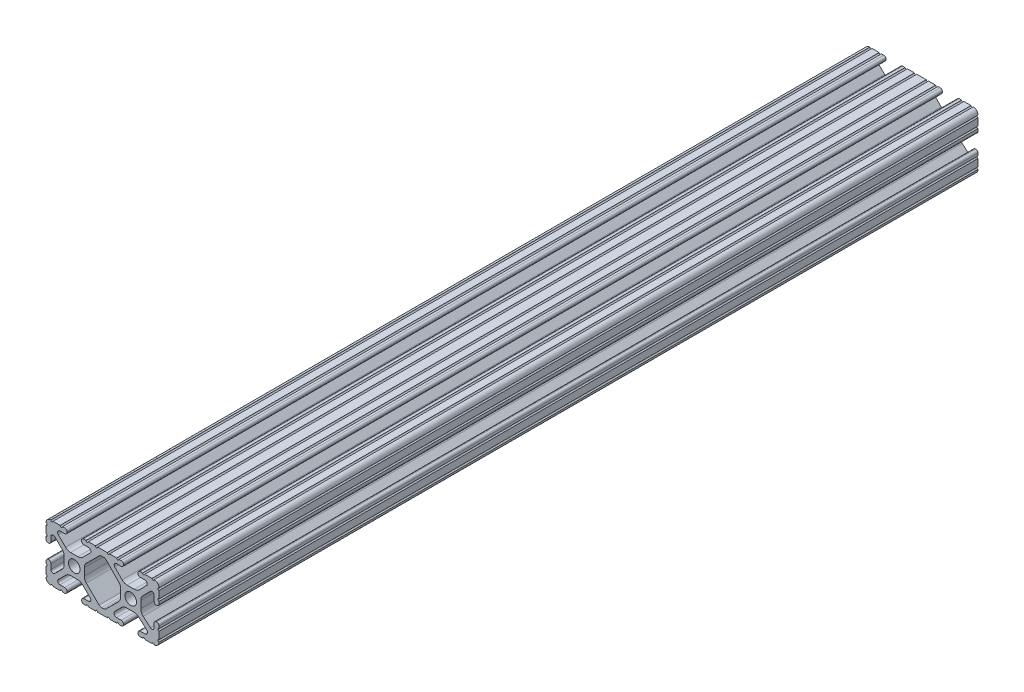
SolidWorks part; units mm, degrees
ref_plane "Front Plane" through (0, 0, 0) normal (0, 0, 1) x (1, 0, 0)
ref_plane "Top Plane" through (0, 0, 0) normal (0, 1, 0) x (1, 0, 0)
ref_plane "Right Plane" through (0, 0, 0) normal (1, 0, 0) x (0, 0, -1)
sketch "Sketch1" plane through (0, 0, 0) normal (0, 0, 1) x (1, 0, 0)
  line L0 (-7.2595, -3.8694) -> (-1.5457, -9.5728)
  line L1 (-8.1915, 1.6223) -> (-8.1915, -1.6223)
  line L2 (-1.504, 9.5765) -> (-7.252, 3.8768)
  line L3 (0.5515, 10.033) -> (-0.3952, 10.033)
  line L4 (7.2829, 3.8459) -> (1.6756, 9.5611)
  line L5 (8.1915, -1.6223) -> (8.1915, 1.6223)
  line L6 (1.5457, -9.5728) -> (7.2595, -3.8694)
  line L7 (-0.4332, -10.033) -> (0.4332, -10.033)
  line L8 (18.0171, 12.7) -> (16.9875, 12.7)
  line L9 (15.9385, 11.651) -> (15.9385, 11.5392)
  line L10 (16.9875, 10.4902) -> (19.1164, 10.4902)
  line L11 (19.8441, 8.7652) -> (16.619, 5.4551)
  line L12 (14.3449, 4.4958) -> (11.0833, 4.4958)
  line L13 (8.817, 5.4472) -> (5.5642, 8.7627)
  line L14 (6.2894, 10.4902) -> (8.4125, 10.4902)
  line L15 (9.4615, 11.5392) -> (9.4615, 11.651)
  line L16 (8.4125, 12.7) -> (7.3829, 12.7)
  line L17 (6.3669, 12.7) -> (3.1496, 12.7)
  line L18 (2.1336, 12.7) -> (-2.1336, 12.7)
  line L19 (-3.1496, 12.7) -> (-6.3669, 12.7)
  line L20 (-7.3829, 12.7) -> (-8.4125, 12.7)
  line L21 (-9.4615, 11.651) -> (-9.4615, 11.5392)
  line L22 (-8.4125, 10.4902) -> (-6.2836, 10.4902)
  line L23 (-5.5326, 8.6661) -> (-8.81, 5.4163)
  line L24 (-11.0455, 4.4958) -> (-14.3545, 4.4958)
  line L25 (-16.59, 5.4163) -> (-19.8674, 8.6661)
  line L26 (-19.1164, 10.4902) -> (-16.9875, 10.4902)
  line L27 (-15.9385, 11.5392) -> (-15.9385, 11.651)
  line L28 (-16.9875, 12.7) -> (-18.0171, 12.7)
  line L29 (-19.0331, 12.7) -> (-22.2504, 12.7)
  line L30 (-25.4, 9.5504) -> (-25.4, 6.3331)
  line L31 (-25.4, 5.3171) -> (-25.4, 4.2375)
  line L32 (-24.401, 3.2385) -> (-24.2392, 3.2385)
  line L33 (-23.1902, 4.2875) -> (-23.1902, 6.3347)
  line L34 (-21.434, 7.0665) -> (-18.148, 3.8082)
  line L35 (-17.2085, 1.5536) -> (-17.2085, -1.6952)
  line L36 (-18.1405, -3.9423) -> (-21.4316, -7.2274)
  line L37 (-23.1902, -6.498) -> (-23.1902, -4.2875)
  line L38 (-24.2392, -3.2385) -> (-24.351, -3.2385)
  line L39 (-25.4, -4.2875) -> (-25.4, -5.3171)
  line L40 (-25.4, -6.3331) -> (-25.4, -9.5504)
  line L41 (-22.2504, -12.7) -> (-19.0331, -12.7)
  line L42 (-18.0171, -12.7) -> (-16.9875, -12.7)
  line L43 (-15.9384, -11.651) -> (-15.9384, -11.5392)
  line L44 (-16.9875, -10.4902) -> (-19.1164, -10.4902)
  line L45 (-19.8341, -8.7551) -> (-16.4966, -5.4237)
  line L46 (-14.2536, -4.4958) -> (-11.1464, -4.4958)
  line L47 (-8.9034, -5.4237) -> (-5.5659, -8.7551)
  line L48 (-6.2836, -10.4902) -> (-8.4125, -10.4902)
  line L49 (-9.4616, -11.5392) -> (-9.4616, -11.651)
  line L50 (-8.4125, -12.7) -> (-7.3829, -12.7)
  line L51 (-6.3669, -12.7) -> (-3.1496, -12.7)
  line L52 (-2.1336, -12.7) -> (2.1336, -12.7)
  line L53 (3.1496, -12.7) -> (6.3669, -12.7)
  line L54 (7.3829, -12.7) -> (8.4125, -12.7)
  line L55 (9.4616, -11.651) -> (9.4616, -11.5392)
  line L56 (8.4125, -10.4902) -> (6.2894, -10.4902)
  line L57 (5.4807, -8.5353) -> (8.5979, -5.4237)
  line L58 (10.8409, -4.4958) -> (14.1026, -4.4958)
  line L59 (16.1879, -5.2766) -> (19.8682, -8.4822)
  line L60 (19.1164, -10.4902) -> (16.9875, -10.4902)
  line L61 (15.9384, -11.5392) -> (15.9384, -11.651)
  line L62 (16.9875, -12.7) -> (18.0171, -12.7)
  line L63 (19.0331, -12.7) -> (22.2504, -12.7)
  line L64 (25.4, -9.5504) -> (25.4, -6.3331)
  line L65 (25.4, -5.3171) -> (25.4, -4.2375)
  line L66 (24.401, -3.2385) -> (24.1892, -3.2385)
  line L67 (23.1902, -4.2375) -> (23.1902, -6.1559)
  line L68 (21.584, -6.8869) -> (18.2982, -4.025)
  line L69 (17.2085, -1.6308) -> (17.2085, 1.6308)
  line L70 (18.1094, 3.8465) -> (21.5263, 7.3534)
  line L71 (23.1902, 6.6769) -> (23.1902, 4.2375)
  line L72 (24.1892, 3.2385) -> (24.401, 3.2385)
  line L73 (25.4, 4.2375) -> (25.4, 5.3171)
  line L74 (25.4, 6.3332) -> (25.4, 9.5504)
  line L75 (22.2504, 12.7) -> (19.0331, 12.7)
  circle A0 centre (-12.7, 0) radius 2.6035
  circle A1 centre (12.7, 0) radius 2.6035
  arc A2 (-1.5457, -9.5728) -> (-0.4332, -10.033) centre (-0.4332, -8.4582) ccw
  arc A3 (-8.1915, -1.6223) -> (-7.2595, -3.8694) centre (-5.0165, -1.6223) ccw
  arc A4 (-7.252, 3.8768) -> (-8.1915, 1.6223) centre (-5.0165, 1.6223) ccw
  arc A5 (-0.3952, 10.033) -> (-1.504, 9.5765) centre (-0.3952, 8.4582) ccw
  arc A6 (1.6756, 9.5611) -> (0.5515, 10.033) centre (0.5515, 8.4582) ccw
  arc A7 (8.1915, 1.6223) -> (7.2829, 3.8459) centre (5.0165, 1.6223) ccw
  arc A8 (7.2595, -3.8694) -> (8.1915, -1.6223) centre (5.0165, -1.6223) ccw
  arc A9 (0.4332, -10.033) -> (1.5457, -9.5728) centre (0.4332, -8.4582) ccw
  arc A10 (18.0171, 12.7) -> (19.0331, 12.7) centre (18.5251, 12.7) ccw
  arc A11 (16.9875, 12.7) -> (15.9385, 11.651) centre (16.9875, 11.651) ccw
  arc A12 (15.9385, 11.5392) -> (16.9875, 10.4902) centre (16.9875, 11.5392) ccw
  arc A13 (19.8441, 8.7652) -> (19.1164, 10.4902) centre (19.1164, 9.4742) ccw
  arc A14 (14.3449, 4.4958) -> (16.619, 5.4551) centre (14.3449, 7.6708) ccw
  arc A15 (8.817, 5.4472) -> (11.0833, 4.4958) centre (11.0833, 7.6708) ccw
  arc A16 (6.2894, 10.4902) -> (5.5642, 8.7627) centre (6.2894, 9.4742) ccw
  arc A17 (8.4125, 10.4902) -> (9.4615, 11.5392) centre (8.4125, 11.5392) ccw
  arc A18 (9.4615, 11.651) -> (8.4125, 12.7) centre (8.4125, 11.651) ccw
  arc A19 (6.3669, 12.7) -> (7.3829, 12.7) centre (6.8749, 12.7) ccw
  arc A20 (2.1336, 12.7) -> (3.1496, 12.7) centre (2.6416, 12.7) ccw
  arc A21 (-3.1496, 12.7) -> (-2.1336, 12.7) centre (-2.6416, 12.7) ccw
  arc A22 (-7.3829, 12.7) -> (-6.3669, 12.7) centre (-6.8749, 12.7) ccw
  arc A23 (-8.4125, 12.7) -> (-9.4615, 11.651) centre (-8.4125, 11.651) ccw
  arc A24 (-9.4615, 11.5392) -> (-8.4125, 10.4902) centre (-8.4125, 11.5392) ccw
  arc A25 (-5.5326, 8.6661) -> (-6.2836, 10.4902) centre (-6.2836, 9.4235) ccw
  arc A26 (-11.0455, 4.4958) -> (-8.81, 5.4163) centre (-11.0455, 7.6708) ccw
  arc A27 (-16.59, 5.4163) -> (-14.3545, 4.4958) centre (-14.3545, 7.6708) ccw
  arc A28 (-19.1164, 10.4902) -> (-19.8674, 8.6661) centre (-19.1164, 9.4235) ccw
  arc A29 (-16.9875, 10.4902) -> (-15.9385, 11.5392) centre (-16.9875, 11.5392) ccw
  arc A30 (-15.9385, 11.651) -> (-16.9875, 12.7) centre (-16.9875, 11.651) ccw
  arc A31 (-19.0331, 12.7) -> (-18.0171, 12.7) centre (-18.5251, 12.7) ccw
  arc A32 (-23.2664, 12.6998) -> (-22.2504, 12.7) centre (-22.7584, 12.7) ccw
  arc A33 (-23.2664, 12.6998) -> (-25.3998, 10.5664) centre (-23.2918, 10.5918) ccw
  arc A34 (-25.4, 9.5504) -> (-25.3998, 10.5664) centre (-25.4, 10.0584) ccw
  arc A35 (-25.4, 5.3171) -> (-25.4, 6.3331) centre (-25.4, 5.8251) ccw
  arc A36 (-25.4, 4.2375) -> (-24.401, 3.2385) centre (-24.401, 4.2375) ccw
  arc A37 (-24.2392, 3.2385) -> (-23.1902, 4.2875) centre (-24.2392, 4.2875) ccw
  arc A38 (-21.434, 7.0665) -> (-23.1902, 6.3347) centre (-22.1596, 6.3347) ccw
  arc A39 (-17.2085, 1.5536) -> (-18.148, 3.8082) centre (-20.3835, 1.5536) ccw
  arc A40 (-18.1405, -3.9423) -> (-17.2085, -1.6952) centre (-20.3835, -1.6952) ccw
  arc A41 (-23.1902, -6.498) -> (-21.4316, -7.2274) centre (-22.1596, -6.498) ccw
  arc A42 (-23.1902, -4.2875) -> (-24.2392, -3.2385) centre (-24.2392, -4.2875) ccw
  arc A43 (-24.351, -3.2385) -> (-25.4, -4.2875) centre (-24.351, -4.2875) ccw
  arc A44 (-25.4, -6.3331) -> (-25.4, -5.3171) centre (-25.4, -5.8251) ccw
  arc A45 (-25.3998, -10.5664) -> (-25.4, -9.5504) centre (-25.4, -10.0584) ccw
  arc A46 (-25.3998, -10.5664) -> (-23.2664, -12.6998) centre (-23.2918, -10.5918) ccw
  arc A47 (-22.2504, -12.7) -> (-23.2664, -12.6998) centre (-22.7584, -12.7) ccw
  arc A48 (-18.0171, -12.7) -> (-19.0331, -12.7) centre (-18.5251, -12.7) ccw
  arc A49 (-16.9875, -12.7) -> (-15.9384, -11.651) centre (-16.9875, -11.651) ccw
  arc A50 (-15.9384, -11.5392) -> (-16.9875, -10.4902) centre (-16.9875, -11.5392) ccw
  arc A51 (-19.8341, -8.7551) -> (-19.1164, -10.4902) centre (-19.1164, -9.4742) ccw
  arc A52 (-14.2536, -4.4958) -> (-16.4966, -5.4237) centre (-14.2536, -7.6708) ccw
  arc A53 (-8.9034, -5.4237) -> (-11.1464, -4.4958) centre (-11.1464, -7.6708) ccw
  arc A54 (-6.2836, -10.4902) -> (-5.5659, -8.7551) centre (-6.2836, -9.4742) ccw
  arc A55 (-8.4125, -10.4902) -> (-9.4616, -11.5392) centre (-8.4125, -11.5392) ccw
  arc A56 (-9.4616, -11.651) -> (-8.4125, -12.7) centre (-8.4125, -11.651) ccw
  arc A57 (-6.3669, -12.7) -> (-7.3829, -12.7) centre (-6.8749, -12.7) ccw
  arc A58 (-2.1336, -12.7) -> (-3.1496, -12.7) centre (-2.6416, -12.7) ccw
  arc A59 (3.1496, -12.7) -> (2.1336, -12.7) centre (2.6416, -12.7) ccw
  arc A60 (7.3829, -12.7) -> (6.3669, -12.7) centre (6.8749, -12.7) ccw
  arc A61 (8.4125, -12.7) -> (9.4616, -11.651) centre (8.4125, -11.651) ccw
  arc A62 (9.4616, -11.5392) -> (8.4125, -10.4902) centre (8.4125, -11.5392) ccw
  arc A63 (5.4807, -8.5353) -> (6.2894, -10.4902) centre (6.2894, -9.3455) ccw
  arc A64 (10.8409, -4.4958) -> (8.5979, -5.4237) centre (10.8409, -7.6708) ccw
  arc A65 (16.1879, -5.2766) -> (14.1026, -4.4958) centre (14.1026, -7.6708) ccw
  arc A66 (19.1164, -10.4902) -> (19.8682, -8.4822) centre (19.1164, -9.3455) ccw
  arc A67 (16.9875, -10.4902) -> (15.9384, -11.5392) centre (16.9875, -11.5392) ccw
  arc A68 (15.9384, -11.651) -> (16.9875, -12.7) centre (16.9875, -11.651) ccw
  arc A69 (19.0331, -12.7) -> (18.0171, -12.7) centre (18.5251, -12.7) ccw
  arc A70 (23.2664, -12.6998) -> (22.2504, -12.7) centre (22.7584, -12.7) ccw
  arc A71 (23.2664, -12.6998) -> (25.3998, -10.5664) centre (23.2918, -10.5918) ccw
  arc A72 (25.4, -9.5504) -> (25.3998, -10.5664) centre (25.4, -10.0584) ccw
  arc A73 (25.4, -5.3171) -> (25.4, -6.3331) centre (25.4, -5.8251) ccw
  arc A74 (25.4, -4.2375) -> (24.401, -3.2385) centre (24.401, -4.2375) ccw
  arc A75 (24.1892, -3.2385) -> (23.1902, -4.2375) centre (24.1892, -4.2375) ccw
  arc A76 (21.584, -6.8869) -> (23.1902, -6.1559) centre (22.2207, -6.1559) ccw
  arc A77 (17.2085, -1.6308) -> (18.2982, -4.025) centre (20.3835, -1.6308) ccw
  arc A78 (18.1094, 3.8465) -> (17.2085, 1.6308) centre (20.3835, 1.6308) ccw
  arc A79 (23.1902, 6.6769) -> (21.5263, 7.3534) centre (22.2207, 6.6769) ccw
  arc A80 (23.1902, 4.2375) -> (24.1892, 3.2385) centre (24.1892, 4.2375) ccw
  arc A81 (24.401, 3.2385) -> (25.4, 4.2375) centre (24.401, 4.2375) ccw
  arc A82 (25.4, 6.3332) -> (25.4, 5.3171) centre (25.4, 5.8251) ccw
  arc A83 (25.3998, 10.5664) -> (25.4, 9.5504) centre (25.4, 10.0584) ccw
  arc A84 (25.3998, 10.5664) -> (23.2664, 12.6998) centre (23.2918, 10.5918) ccw
  arc A85 (22.2504, 12.7) -> (23.2664, 12.6998) centre (22.7584, 12.7) ccw
  point P248 (0, 10.033)
extrude "Boss-Extrude1" add sketch "Sketch1" along normal mid plane 368.3
sketch "Sketch2" plane through (17.2085, 0, 0) normal (1, 0, 0) x (0, 0, -1)
  line L0 (0, 0) -> (0, 51.7748) construction
  circle A0 centre (39.6875, 0) radius 3.175
  circle A1 centre (65.0875, 0) radius 3.175
  circle A2 centre (-65.0875, 0) radius 3.175
  circle A3 centre (-39.6875, 0) radius 3.175
  point P7 (0, 0)
  dimension "D1" = 6.35
  dimension "D2" = 39.6875
  dimension "D3" = 6.35
  dimension "D4" = 25.4
extrude "Cut-Extrude1" cut sketch "Sketch2" against normal through all both and the other way through all
